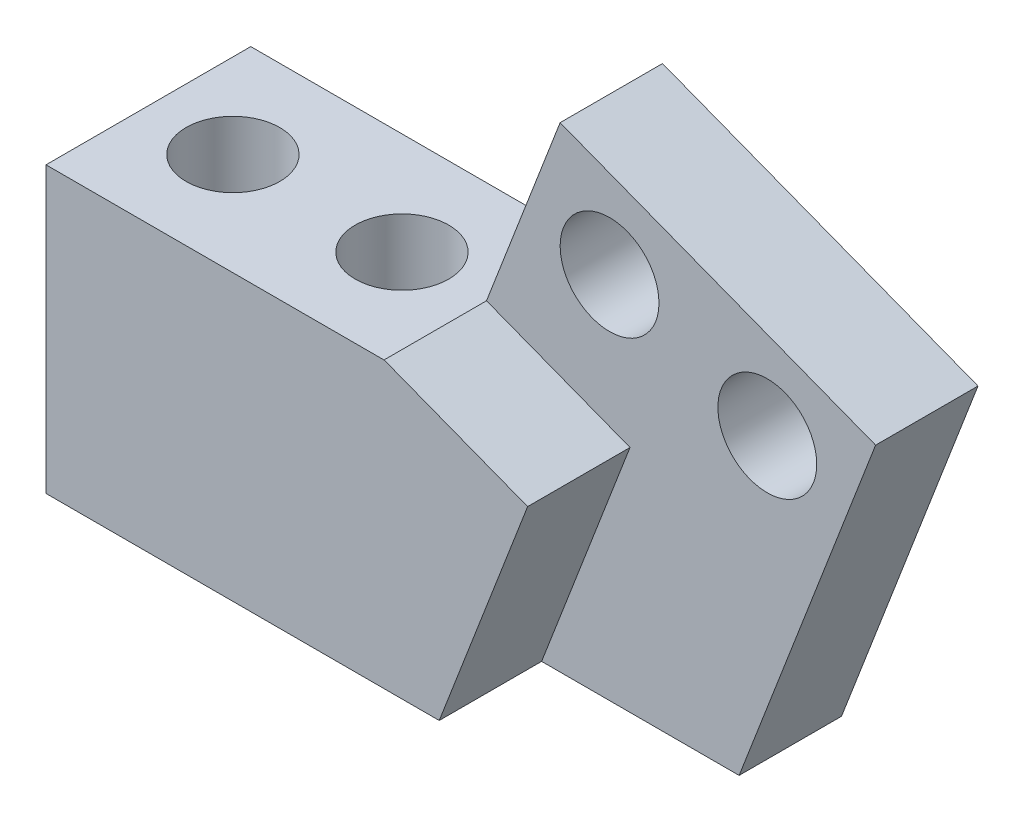
SolidWorks part; units mm, degrees
ref_plane "Front" through (0, 0, 0) normal (0, 0, 1) x (1, 0, 0)
ref_plane "Top" through (0, 0, 0) normal (0, 1, 0) x (1, 0, 0)
ref_plane "Right" through (0, 0, 0) normal (1, 0, 0) x (0, 0, -1)
sketch "Sketch1" plane through (0, 0, 0) normal (0, 0, 1) x (1, 0, 0)
  line L0 (-7.7031, 2.9677) -> (0, 0)
  line L1 (0, 0) -> (7.7031, -2.9677)
  line L2 (-1.9436, 4.731) -> (6.4636, 4.731) construction
  line L3 (0, 0) -> (0, -15.6645) construction
  line L4 (7.7031, -2.9677) -> (1.0375, -20.269)
  line L5 (0, 0) -> (-5.9062, -15.3301) construction
  line L6 (-27.8102, -6.369) -> (-27.8102, -20.269)
  line L7 (-27.8102, -6.369) -> (-11.3002, -6.369)
  line L10 (-27.8102, -20.269) -> (1.0375, -20.269)
  line L11 (-7.7031, 2.9677) -> (-11.3002, -6.369)
  point P7 (1.8227, 4.731)
  dimension "D1" = 21.07
  dimension "D2" = 16.51
  dimension "D3" = 16.51
  dimension "D4" = 25
  dimension "D5" = 13.9
  dimension "D6" = 5.07
extrude "Base-Extrude" add sketch "Sketch1" along normal mid plane 10
sketch "Sketch2" plane through (0, 0, 5) normal (0, 0, 1) x (1, 0, 0)
  line L0 (-7.7031, 2.9677) -> (7.7031, -2.9677)
  line L1 (7.7031, -2.9677) -> (1.0375, -20.269)
  line L2 (1.0375, -20.269) -> (7.7031, -2.9677) construction
  line L3 (-4.2903, -9.0636) -> (-11.2982, -6.3637)
  line L4 (-7.7031, 2.9677) -> (-11.2982, -6.3637)
  line L5 (-8.6073, -20.269) -> (-4.2903, -9.0636)
  line L7 (-8.6073, -20.269) -> (1.0375, -20.269)
  line L8 (-27.8102, -20.269) -> (1.0375, -20.269) construction
  dimension "D1" = 10
  dimension "D2" = 9
extrude "Cutaway for Clamp Plate & Wire" cut sketch "Sketch2" against normal blind 5
sketch "Sketch3" plane through (0, 0, 0) normal (0, 0, 1) x (1, 0, 0)
  line L0 (0, 0) -> (-2.873, -7.4572) construction
  line L1 (7.7031, -2.9677) -> (-7.7031, 2.9677) construction
  circle A0 centre (2.4135, -5.2164) radius 2.413
  circle A1 centre (-5.2896, -2.2487) radius 2.413
  dimension "D1" = 4.826
  dimension "D4" = 4.1275
  dimension "D2" = 90
  dimension "D3" = 4
extrude "Clamp Plate Holes (altered to #10-24 OCT04)" cut sketch "Sketch3" against normal up to surface (5 mm away) up to face at (-10.9805, -8.8793, -5)
sketch "Sketch4" plane through (0, -6.369, 0) normal (0, 1, 0) x (-1, 0, 0)
  line L0 (19.5552, -5) -> (19.5552, 5) construction
  line L1 (11.3002, -5) -> (27.8102, -5) construction
  line L2 (11.3002, 5) -> (27.8102, 5) construction
  line L3 (27.8102, 0) -> (19.5552, 0) construction
  line L5 (27.8102, 5) -> (27.8102, -5) construction
  circle A0 centre (23.6827, 0) radius 2.286
  circle A1 centre (15.4277, 0) radius 2.286
  dimension "D1" = 4.572
extrude "Holes to Pitch Plate" cut sketch "Sketch4" against normal up to surface (13.9 mm away)
